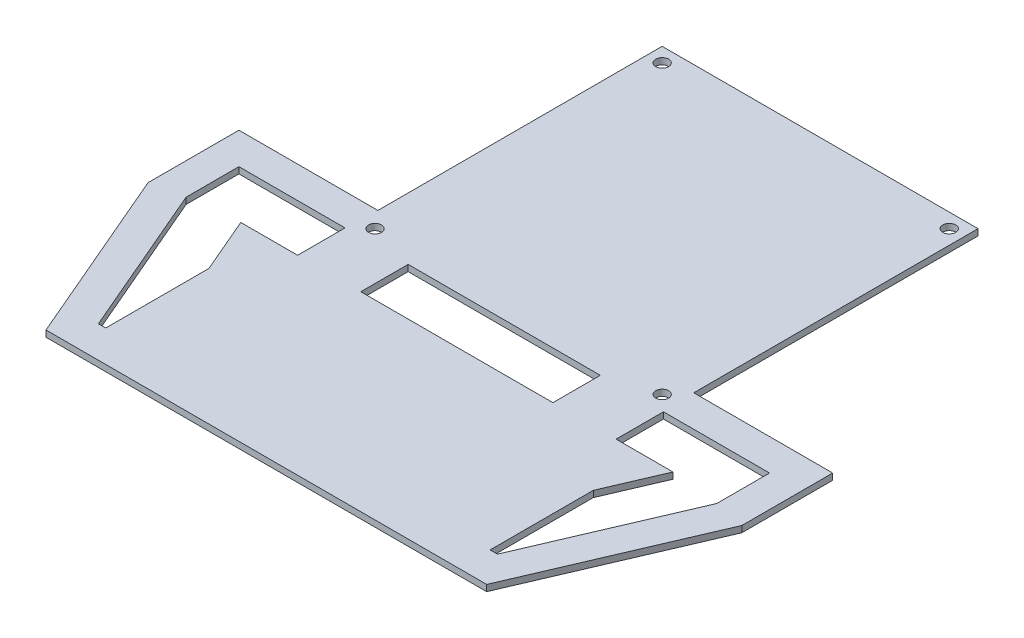
SolidWorks part; units mm, degrees
other "Marca1"
sketch "Croquis6" plane through (-94, 2, 114.9827) normal (0, 1, 0) x (-1, 0, 0)
ref_plane "Alzado" through (0, 0, 0) normal (0, 0, 1) x (1, 0, 0)
ref_plane "Planta" through (0, 0, 0) normal (0, 1, 0) x (1, 0, 0)
ref_plane "Vista lateral" through (0, 0, 0) normal (1, 0, 0) x (0, 0, -1)
sketch "Croquis1" plane through (0, 0, 0) normal (0, 1, 0) x (1, 0, 0)
  line L1 (50, -50) -> (-50, -50) construction
  line L2 (50, -55) -> (50, 50)
  line L3 (50, 50) -> (-50, 50)
  line L4 (-50, -55) -> (-50, 50)
  line L5 (50, -50) -> (-50, 50) construction
  line L6 (50, 50) -> (-50, -50) construction
  line L7 (50, -40) -> (100, -40) construction
  line L8 (69.76, -125.32) -> (-69.76, -125.32)
  line L10 (94, -68.7685) -> (94, -40) construction
  line L11 (-50, -55) -> (50, -55) construction
  line L16 (0, 50) -> (0, -125.32) construction
  line L17 (40, -40) -> (94, -40)
  line L18 (94, -40) -> (94, -68.7685)
  line L19 (-40, -40) -> (-94, -40)
  line L20 (-94, -40) -> (-94, -68.7685)
  line L22 (-50, -40) -> (-100, -40) construction
  line L23 (69.76, -125.32) -> (94, -68.7685)
  line L24 (-69.76, -125.32) -> (-94, -68.7685)
  point P0 (0, 0)
  dimension "D1" = 100
  dimension "D2" = 100
  dimension "D3" = 175.32
  dimension "D4" = 139.52
extrude "Saliente-Extruir1" add sketch "Croquis1" along normal blind 2
sketch "Croquis2" plane through (0, 2, 0) normal (0, 1, 0) x (1, 0, 0)
  line L0 (0, -115) -> (0, 50) construction
  line L1 (50, 50) -> (-50, 50) construction
  line L3 (-50, 0) -> (50, 0) construction
  line L5 (-50, -40) -> (-50, 50) construction
  line L7 (50, -50) -> (-50, -50) construction
  circle A0 centre (-45.45, -45.45) radius 2.05
  circle A1 centre (45.45, -45.45) radius 2.05
  circle A2 centre (-45.45, 45.45) radius 2.05
  circle A3 centre (45.45, 45.45) radius 2.05
  dimension "D1" = 4.1
  dimension "D2" = 4.55
  dimension "D3" = 100
  dimension "D4" = 4.55
  dimension "D5" = 50
  dimension "D6" = 90.9
extrude "Cortar-Extruir1" cut sketch "Croquis2" against normal through all
sketch "Croquis7" plane through (0, 2, 0) normal (0, 1, 0) x (1, 0, 0)
  line L0 (53.2761, -100.32) -> (-53.2761, -100.32) construction
  line L1 (-60.8458, -82.66) -> (-60.8458, -115.32)
  line L2 (-60.8458, -115.32) -> (-63.1664, -115.32)
  line L3 (50.4155, -40) -> (94, -40)
  line L4 (94, -40) -> (94, -68.7685)
  line L5 (69.76, -125.32) -> (94, -68.7685)
  line L6 (50.4155, -50) -> (84, -50)
  line L7 (84, -50) -> (84, -66.7156)
  line L8 (63.1664, -115.32) -> (84, -66.7156)
  line L9 (63.1664, -115.32) -> (-63.1664, -115.32) construction
  line L10 (69.76, -125.32) -> (-69.76, -125.32)
  line L11 (63.1664, -115.32) -> (60.8458, -115.32)
  line L12 (-63.1664, -115.32) -> (-84, -66.7156)
  line L13 (-84, -50) -> (-84, -66.7156)
  line L14 (-50.4155, -65) -> (-50.4155, -50)
  line L15 (53.2761, -100.32) -> (68.4155, -65) construction
  line L16 (-53.2761, -100.32) -> (-68.4155, -65) construction
  line L17 (-94, -40) -> (-94, -68.7685)
  line L18 (-69.76, -125.32) -> (-94, -68.7685)
  line L19 (50.4155, -65) -> (68.4155, -65)
  line L20 (68.4155, -65) -> (68.4155, -65)
  line L21 (60.8458, -82.66) -> (68.4155, -65)
  line L22 (50.4155, -65) -> (50.4155, -50)
  line L23 (-60.8458, -82.66) -> (-68.4155, -65)
  line L24 (-68.4155, -65) -> (-68.4155, -65)
  line L25 (-50, -40) -> (-94, -40) construction
  line L26 (-50, -40) -> (-94, -40)
  line L27 (-50, -65) -> (-68.4155, -65)
  line L28 (50.4155, -50) -> (-84, -50)
  line L29 (50.4155, -65) -> (-50, -65)
  line L30 (60.8458, -82.66) -> (60.8458, -115.32)
  line L31 (0, 50) -> (0, -131.3249) construction
  line L32 (50, 50) -> (-50, 50) construction
  line L33 (30.4155, -65) -> (30.4155, -50)
  line L34 (-50, -50) -> (-84, -50) construction
  line L35 (-30.4155, -65) -> (-30.4155, -50)
  point P31 (0, 0)
  dimension "D3" = 18
  dimension "D4" = 20
  dimension "D1" = 10
  dimension "D2" = 15
extrude "Cortar-Extruir2" cut sketch "Croquis7" against normal blind 5 and the other way through all
